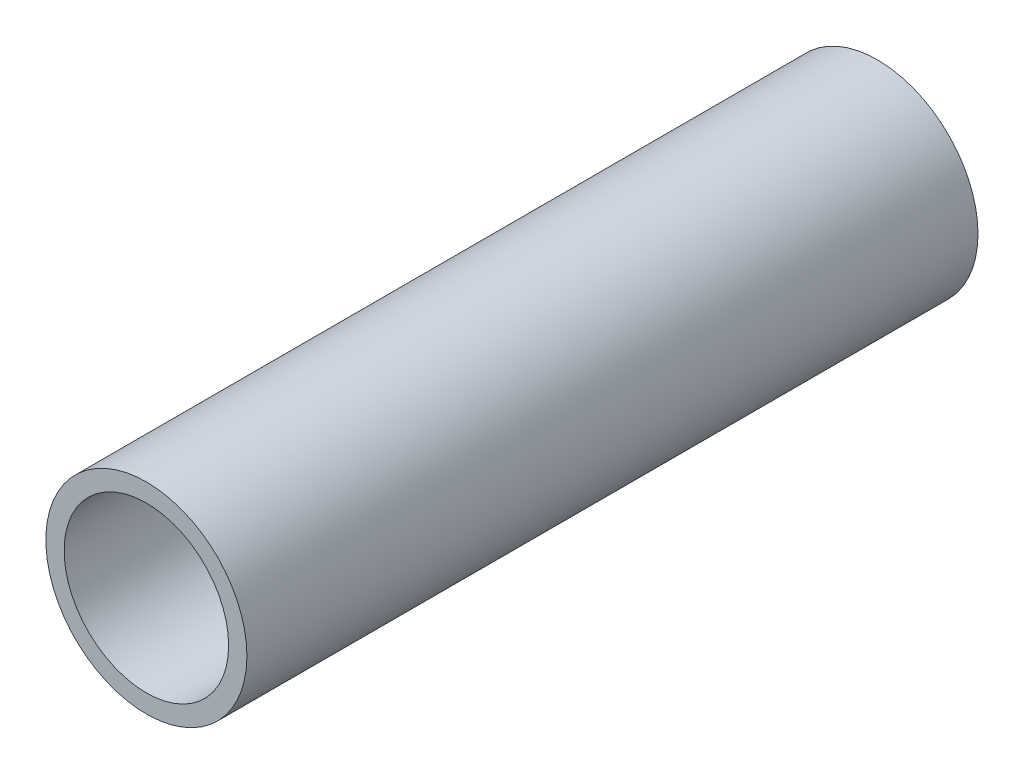
SolidWorks part; units mm, degrees
material "AISI 304"
ref_plane "Front Plane" through (0, 0, 0) normal (0, 0, 1) x (1, 0, 0)
ref_plane "Top Plane" through (0, 0, 0) normal (0, 1, 0) x (1, 0, 0)
ref_plane "Right Plane" through (0, 0, 0) normal (1, 0, 0) x (0, 0, -1)
sketch "Sketch1" plane through (0, 0, 0) normal (1, 0, 0) x (0, 0, -1)
  line L0 (-40, 9) -> (40, 9)
  line L1 (-40, -11) -> (-40, 11) construction
  line L2 (-40, 11) -> (40, 11)
  line L3 (40, 11) -> (40, -11) construction
  line L4 (-40, -11) -> (40, -11) construction
  line L5 (0, 0) -> (0, 11) construction
  line L6 (40, 9) -> (40, 11)
  line L7 (-40, 9) -> (-40, 11)
  line L8 (0, 0) -> (40, 0) construction
  point P9 (-40, 9)
  dimension "D1" = 22
  dimension "D2" = 80
  dimension "D3" = 18
revolve "Revolve1" add sketch "Sketch1" angle 360 about L8
